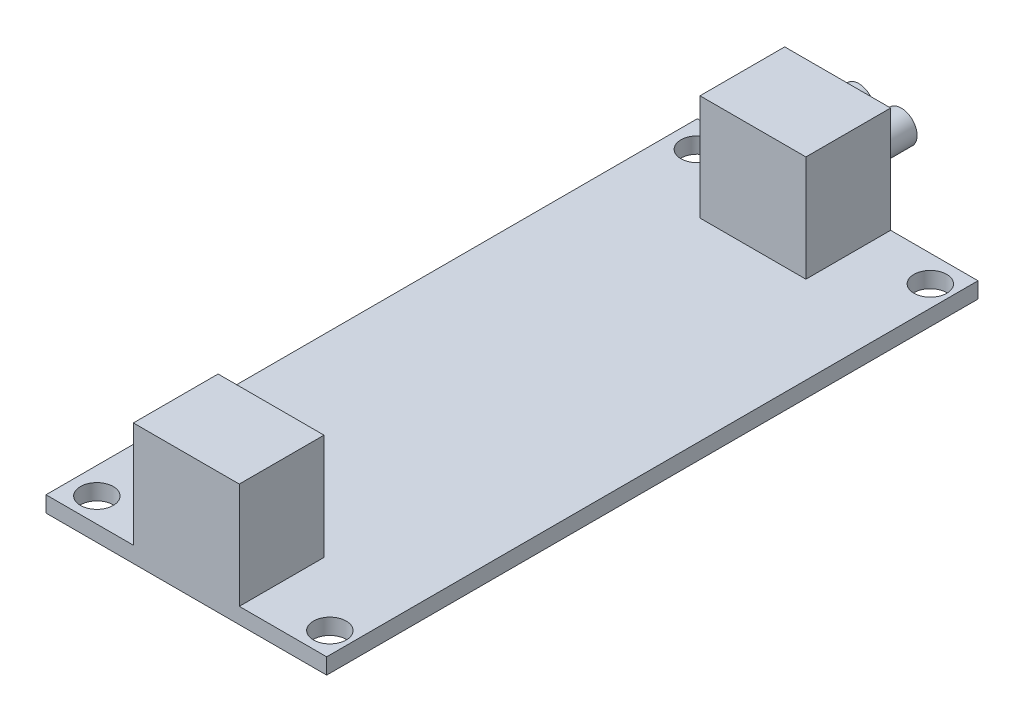
SolidWorks part; units mm, degrees
ref_plane "Ebene vorne" through (0, 0, 0) normal (0, 0, 1) x (1, 0, 0)
ref_plane "Ebene oben" through (0, 0, 0) normal (0, 1, 0) x (1, 0, 0)
ref_plane "Ebene rechts" through (0, 0, 0) normal (1, 0, 0) x (0, 0, -1)
sketch "Skizze1" plane through (0, 0, 0) normal (0, 1, 0) x (1, 0, 0)
  line L1 (-13.25, 30.75) -> (13.25, 30.75)
  line L2 (-13.25, 30.75) -> (-13.25, -30.75)
  line L3 (-13.25, -30.75) -> (13.25, -30.75)
  line L4 (13.25, 30.75) -> (13.25, -30.75)
  line L5 (-13.25, 30.75) -> (13.25, -30.75) construction
  line L6 (-13.25, -30.75) -> (13.25, 30.75) construction
  point P0 (0, 0)
  dimension "D1" = 61.5
  dimension "D2" = 26.5
extrude "Aufsatz-Linear austragen1" add sketch "Skizze1" along normal blind 1.5
sketch "Skizze2" plane through (0, 1.5, 0) normal (0, 1, 0) x (1, 0, 0)
  line L0 (-13.25, 30.75) -> (-13.25, -30.75) construction
  line L1 (-10.75, 28.25) -> (11.25, 28.25) construction
  line L2 (-10.75, 28.25) -> (-10.75, -28.45) construction
  line L3 (-10.75, -28.45) -> (11.25, -28.45) construction
  line L4 (11.25, 28.25) -> (11.25, -28.45) construction
  line L5 (-10.75, 28.25) -> (11.25, -28.45) construction
  line L6 (-10.75, -28.45) -> (11.25, 28.25) construction
  line L7 (13.25, -30.75) -> (13.25, 30.75) construction
  line L8 (13.25, 30.75) -> (-13.25, 30.75) construction
  line L9 (-13.25, -30.75) -> (13.25, -30.75) construction
  circle A0 centre (-10.75, 28.25) radius 1.55
  circle A1 centre (11.25, 28.25) radius 1.55
  circle A2 centre (11.25, -28.45) radius 1.55
  circle A3 centre (-10.75, -28.45) radius 1.55
  point P0 (0, 0)
  dimension "D5" = 3.1
  dimension "D1" = 2.5
  dimension "D2" = 2
  dimension "D3" = 2.5
  dimension "D4" = 2.3
extrude "Schnitt-Linear austragen1" cut sketch "Skizze2" against normal through all
sketch "Skizze3" plane through (0, 1.5, 0) normal (0, 1, 0) x (1, 0, 0)
  line L0 (0, 30.75) -> (0, -30.75) construction
  line L1 (13.25, 30.75) -> (-13.25, 30.75) construction
  line L2 (-13.25, -30.75) -> (13.25, -30.75) construction
  line L4 (5, -22.75) -> (-5, -22.75)
  line L5 (5, -22.75) -> (5, -30.75)
  line L6 (5, -30.75) -> (-5, -30.75)
  line L7 (-5, -22.75) -> (-5, -30.75)
  line L8 (5, -22.75) -> (-5, -30.75) construction
  line L9 (5, -30.75) -> (-5, -22.75) construction
  line L10 (5, 22.75) -> (-5, 22.75)
  line L11 (5, 22.75) -> (5, 30.75)
  line L12 (5, 30.75) -> (-5, 30.75)
  line L13 (-5, 22.75) -> (-5, 30.75)
  line L14 (5, 22.75) -> (-5, 30.75) construction
  line L15 (5, 30.75) -> (-5, 22.75) construction
  point P6 (0, -26.75)
  point P11 (0, 26.75)
  dimension "D1" = 8
  dimension "D2" = 10
extrude "Aufsatz-Linear austragen2" add sketch "Skizze3" along normal blind 10
sketch "Skizze4" plane through (0, 0, -30.75) normal (0, 0, -1) x (-1, 0, 0)
  line L0 (-2, 6.5) -> (2, 6.5) construction
  line L3 (0, 11.5) -> (0, 0) construction
  line L4 (-5, 11.5) -> (5, 11.5) construction
  circle A0 centre (-2, 6.5) radius 1.5
  circle A1 centre (2, 6.5) radius 1.5
  point P2 (0, 6.5)
  dimension "D1" = 3
  dimension "D2" = 4
  dimension "D3" = 5
extrude "Aufsatz-Linear austragen3" add sketch "Skizze4" along normal blind 4
